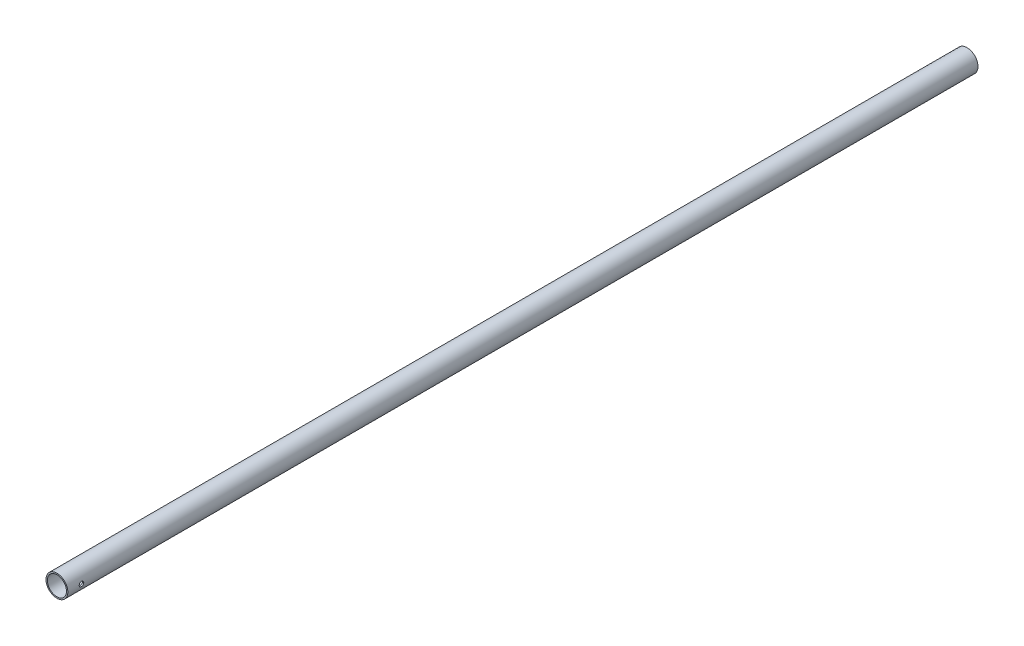
SolidWorks part; units mm, degrees
ref_plane "Płaszczyzna przednia" through (0, 0, 0) normal (0, 0, 1) x (1, 0, 0)
ref_plane "Płaszczyzna górna" through (0, 0, 0) normal (0, 1, 0) x (1, 0, 0)
ref_plane "Płaszczyzna prawa" through (0, 0, 0) normal (1, 0, 0) x (0, 0, -1)
sketch "Szkic1" plane through (0, 0, 0) normal (0, 0, 1) x (1, 0, 0)
  circle A0 centre (0, 0) radius 24
  circle A1 centre (0, 0) radius 21
  dimension "D1" = 42
  dimension "50" = 48
extrude "Dodanie-wyciągnięcie1" add sketch "Szkic1" along normal blind 2000
hole_wizard "Otwory ustalające Ø10.0mm2" positions "Szkic 3D5" profile "Szkic6" hole size "Ø10.0" standard "BSI" end condition through all
sketch3d "Szkic 3D5"
  point P0 (24, 0, 1970)
sketch "Szkic6" plane through (24, 0, 1970) normal (0, 1, 0) x (0, 0, -1)
  line L0 (0, 0) -> (0, 48)
  line L1 (0, 48) -> (5, 48)
  line L2 (5, 48) -> (5, 0.025)
  line L3 (5, 0.025) -> (5.025, 0)
  line L5 (5.025, 0) -> (0, 0)
  line L6 (-5, 0.025) -> (-5.025, 0) construction
  line L11 (0, -6.35) -> (0, 107.95) construction
  dimension "Średnica otworu na wylot" = 10
  dimension "Głębokość otworu na wylot" = 48
  dimension "Średnica zewnętrznego pogłębienia stożkowego" = 10.05
  dimension "Kąt zewnętrznego pogłębienia stożkowego" = 90
